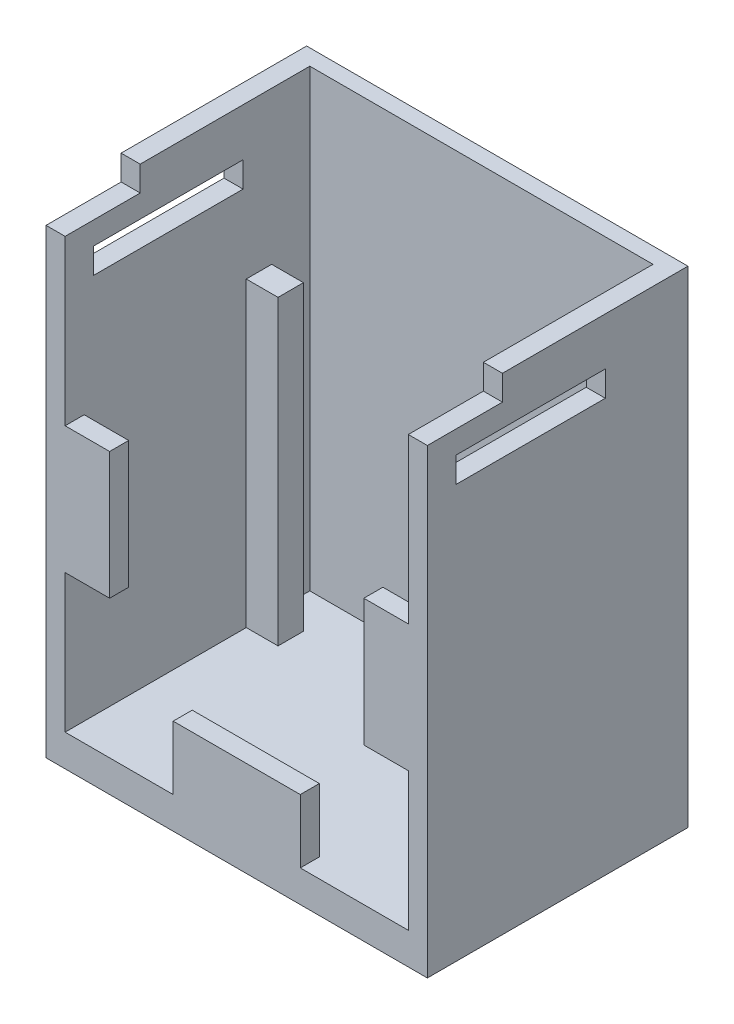
SolidWorks part; units mm, degrees
material "ABS"
ref_plane "Front Plane" through (0, 0, 0) normal (0, 0, 1) x (1, 0, 0)
ref_plane "Top Plane" through (0, 0, 0) normal (0, 1, 0) x (1, 0, 0)
ref_plane "Right Plane" through (0, 0, 0) normal (1, 0, 0) x (0, 0, -1)
sketch "Sketch1" plane through (0, 0, 0) normal (0, 0, 1) x (1, 0, 0)
  line L1 (15.24, -25.4) -> (-15.24, -25.4)
  line L2 (15.24, -25.4) -> (15.24, 15.24)
  line L3 (15.24, 15.24) -> (-15.24, 15.24)
  line L4 (-15.24, -25.4) -> (-15.24, 15.24)
  point P0 (0, 0)
  dimension "D1" = 30.48
  dimension "D2" = 40.64
extrude "Initial Block" add sketch "Sketch1" along normal blind 19.05 and the other way blind 1.778
sketch "Sketch2" plane through (0, 15.24, 0) normal (0, 1, 0) x (1, 0, 0)
  line L0 (15.24, 1.778) -> (-15.24, 1.778) construction
  line L1 (-13.716, 0.508) -> (13.716, 0.508)
  line L2 (-13.716, 0.508) -> (-13.716, -19.05)
  line L3 (-13.716, -19.05) -> (13.716, -19.05)
  line L4 (13.716, 0.508) -> (13.716, -19.05)
  line L5 (0, 1.778) -> (0, -14.7779) construction
  line L6 (15.24, -19.05) -> (-15.24, -19.05) construction
  point P9 (0, 1.778)
  point P11 (0, 0.508)
  point P12 (0, 0.508)
  dimension "D1" = 27.432
  dimension "D2" = 1.27
  dimension "D3" = 0
extrude "Initial Cut" cut sketch "Sketch2" against normal blind 38.1
ref_plane "Plane1" through (0, 0, 19.05) normal (0, 0, 1) x (1, 0, 0)
ref_plane "Plane2" through (0, 0, 0) normal (1, 0, 0) x (0, 0, -1)
sketch "Sketch20" plane through (0, 0, 19.05) normal (0, 0, 1) x (1, 0, 0)
  line L0 (-15.24, 9.398) -> (-15.24, -22.86) construction
  line L1 (-15.24, -22.86) -> (15.24, -22.86) construction
  line L2 (15.24, -22.86) -> (15.24, 9.398) construction
  line L3 (-15.24, -6.731) -> (15.24, -6.731) construction
  line L4 (15.24, 9.398) -> (-15.24, 9.398) construction
  line L5 (-15.24, -11.811) -> (-10.16, -11.811)
  line L6 (-15.24, -11.811) -> (-15.24, -1.651)
  line L7 (-15.24, -1.651) -> (-10.16, -1.651)
  line L8 (-10.16, -11.811) -> (-10.16, -1.651)
  line L9 (0, 9.398) -> (0, -22.86) construction
  line L10 (15.24, -11.811) -> (15.24, -1.651)
  line L11 (-5.08, -17.78) -> (5.08, -17.78)
  line L12 (-5.08, -17.78) -> (-5.08, -22.86)
  line L13 (-5.08, -22.86) -> (5.08, -22.86)
  line L14 (5.08, -17.78) -> (5.08, -22.86)
  line L15 (15.24, -11.811) -> (10.16, -11.811)
  line L16 (10.16, -11.811) -> (10.16, -1.651)
  line L17 (15.24, -1.651) -> (10.16, -1.651)
  line L19 (-13.716, -22.86) -> (13.716, -22.86) construction
  line L23 (-15.24, 15.24) -> (-15.24, -25.4) construction
  line L24 (15.24, -25.4) -> (15.24, 15.24) construction
  dimension "D1" = 10.16
  dimension "D2" = 5.08
  dimension "D3" = 10.16
  dimension "D4" = 5.08
  dimension "D5" = 5.08
  dimension "D6" = 10.16
extrude "Boss-Extrude1" add sketch "Sketch20" against normal blind 1.524
sketch "Sketch21" plane through (-13.716, 0, 0) normal (1, 0, 0) x (0, 0, -1)
  line L0 (-19.05, -1.651) -> (-19.05, 15.24) construction
  line L1 (-4.572, 1.27) -> (-2.54, 1.27)
  line L2 (-4.572, 1.27) -> (-4.572, -22.86)
  line L3 (-4.572, -22.86) -> (-2.54, -22.86)
  line L4 (-2.54, 1.27) -> (-2.54, -22.86)
  line L5 (0.508, 15.24) -> (-19.05, 15.24) construction
  line L6 (0.508, -22.86) -> (-19.05, -22.86) construction
  dimension "D1" = 2.032
  dimension "D2" = 14.478
  dimension "D3" = 13.97
  dimension "D4" = 0
extrude "Boss-Extrude2" add sketch "Sketch21" along normal blind 2.54 contours L4 L3 L2 L1
mirror "Mirror2" about plane through (0, 0, 0) normal (1, 0, 0) of "Boss-Extrude2"
sketch "Sketch27" plane through (15.24, 0, 0) normal (1, 0, 0) x (0, 0, -1)
  line L0 (-16.764, 9.652) -> (-4.826, 9.652)
  line L1 (-16.764, 9.652) -> (-16.764, 7.62)
  line L2 (-16.764, 7.62) -> (-4.826, 7.62)
  line L3 (-4.826, 9.652) -> (-4.826, 7.62)
  line L5 (-19.05, -25.4) -> (-19.05, 15.24) construction
  line L7 (1.778, -25.4) -> (-19.05, -25.4) construction
  dimension "D1" = 11.938
  dimension "D2" = 2.032
  dimension "D3" = 33.02
  dimension "D4" = 2.286
extrude "Cut-Extrude6" cut sketch "Sketch27" against normal up to next (1.524 mm away)
mirror "Mirror6" about plane through (0, 0, 0) normal (1, 0, 0) of "Cut-Extrude6"
sketch "Sketch28" plane through (0, 0, 19.05) normal (0, 0, 1) x (1, 0, 0)
  line L0 (15.24, -25.4) -> (15.24, 15.24) construction
  line L1 (-15.24, 15.24) -> (15.24, 15.24)
  line L2 (-15.24, 15.24) -> (-15.24, 13.462)
  line L3 (-15.24, 13.462) -> (15.24, 13.462)
  line L4 (15.24, 15.24) -> (15.24, 13.462)
  dimension "D1" = 1.778
extrude "Cut-Extrude7" cut sketch "Sketch28" against normal through all
sketch "Sketch29" plane through (0, 0, 19.05) normal (0, 0, 1) x (1, 0, 0)
  line L0 (15.24, -25.4) -> (15.24, 13.462) construction
  line L1 (-15.24, 13.462) -> (15.24, 13.462)
  line L2 (-15.24, 13.462) -> (-15.24, 11.462)
  line L3 (-15.24, 11.462) -> (15.24, 11.462)
  line L4 (15.24, 13.462) -> (15.24, 11.462)
  dimension "D1" = 2
extrude "Cut-Extrude8" cut sketch "Sketch29" against normal blind 6
